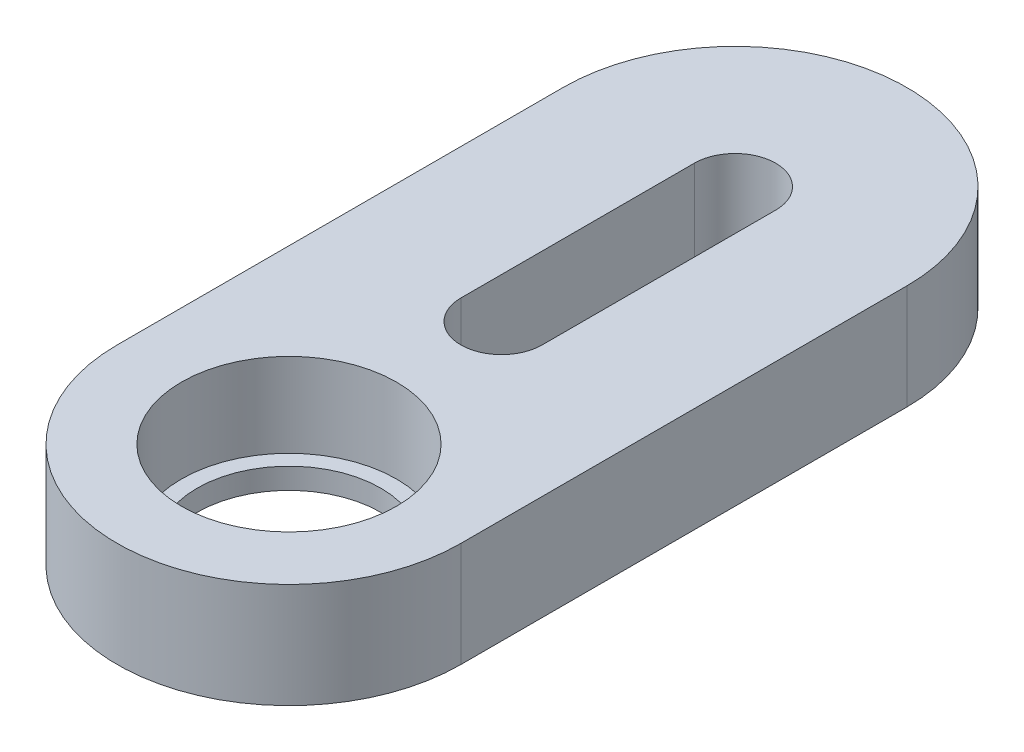
SolidWorks part; units mm, degrees
ref_plane "Front Plane" through (0, 0, 0) normal (0, 0, 1) x (1, 0, 0)
ref_plane "Top Plane" through (0, 0, 0) normal (0, 1, 0) x (1, 0, 0)
ref_plane "Right Plane" through (0, 0, 0) normal (1, 0, 0) x (0, 0, -1)
sketch "Sketch1" plane through (0, 0, 0) normal (0, 1, 0) x (1, 0, 0)
  line L0 (-6.55, 0) -> (-6.55, 17)
  line L1 (6.55, 17) -> (6.55, 0)
  line L2 (0, 17) -> (0, 8.1) construction
  line L3 (1.55, 17) -> (1.55, 8.1)
  line L4 (-1.55, 17) -> (-1.55, 8.1)
  line L5 (0, 18.55) -> (0, 23.55) construction
  line L7 (0, 6.55) -> (0, 4.1) construction
  circle A0 centre (0, 0) radius 4.1
  circle A1 centre (0, 0) radius 6.55
  arc A2 (-6.55, 17) -> (6.55, 17) centre (0, 17) cw
  arc A3 (1.55, 17) -> (-1.55, 17) centre (0, 17) ccw
  arc A4 (-1.55, 8.1) -> (1.55, 8.1) centre (0, 8.1) ccw
  point P8 (0, 12.55)
  point P16 (0, 6.55)
  dimension "D1" = 8.2
  dimension "D2" = 3.1
  dimension "D3" = 5
  dimension "D4" = 12
extrude "Boss-Extrude1" add sketch "Sketch1" along normal blind 4 contours A2 L0 A1 L1 A4 L4 A3 L3 | A1 A0
sketch "Sketch2" plane through (0, 0, 0) normal (0, 1, 0) x (1, 0, 0)
  circle A0 centre (0, 0) radius 4.1
  circle A1 centre (0, 0) radius 4.1 construction
extrude "Boss-Extrude2" add sketch "Sketch2" along normal blind 0.8
sketch "Sketch3" plane through (0, 0.8, 0) normal (0, 1, 0) x (1, 0, 0)
  circle A0 centre (0, 0) radius 3.5
  dimension "D1" = 7
extrude "Cut-Extrude1" cut sketch "Sketch3" against normal through all
